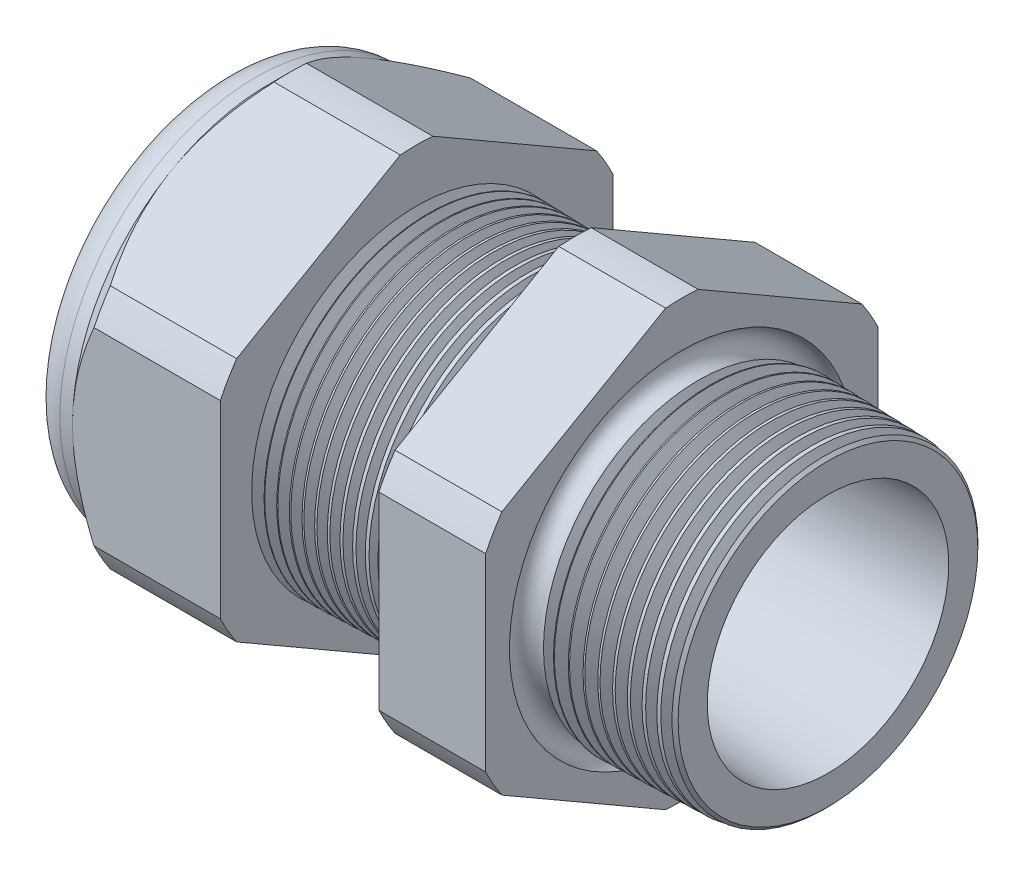
SolidWorks part; units mm, degrees
ref_plane "Front Plane" through (0, 0, 0) normal (0, 0, 1) x (1, 0, 0)
ref_plane "Top Plane" through (0, 0, 0) normal (0, 1, 0) x (1, 0, 0)
ref_plane "Right Plane" through (0, 0, 0) normal (1, 0, 0) x (0, 0, -1)
sketch "Sketch10" plane through (0, 0, 0) normal (0, 0, 1) x (1, 0, 0)
  line L0 (0, 0) -> (-115.3565, 0) construction
  line L1 (-35.814, 5.969) -> (-24.014, 5.969)
  line L2 (1.016, 7.3456) -> (1.016, 9.3776)
  line L3 (-7.874, 9.6104) -> (1.016, 9.3776)
  line L4 (-7.874, 23.876) -> (-7.874, 9.6104)
  line L5 (-7.874, 23.876) -> (-14.374, 23.876)
  line L6 (-14.374, 23.876) -> (-14.374, 9.7806)
  line L7 (-24.014, 10.033) -> (-14.374, 9.7806)
  line L8 (-24.014, 10.033) -> (-24.014, 23.876)
  line L9 (-24.014, 23.876) -> (-33.014, 23.876)
  line L10 (-33.014, 23.876) -> (-33.014, 11.938)
  line L11 (-33.014, 11.938) -> (-35.814, 11.938)
  line L12 (-35.814, 11.938) -> (-35.814, 5.969)
  line L13 (-24.014, 5.969) -> (1.016, 7.3456)
  dimension "D1" = 36.83
  dimension "D2" = 11.938
  dimension "D3" = 1.5
  dimension "D4" = 2.032
  dimension "A" = 20.066
  dimension "D6" = 23.876
  dimension "D8" = 47.752
  dimension "D9" = 2.8
  dimension "D10" = 9
  dimension "D11" = 6.5
  dimension "D" = 8.89
revolve "Revolve2" add sketch "Sketch10" angle 360 about L0
sketch "Sketch12" plane through (-33.014, 0, 0) normal (-1, 0, 0) x (0, 0, 1)
  line L1 (-0.9882, 13.2143) -> (-10.9498, 7.4629)
  line L2 (-11.938, 5.7513) -> (-11.938, -5.7513)
  line L3 (-10.9498, -7.4629) -> (-0.9882, -13.2143)
  line L4 (0.9882, -13.2143) -> (10.9498, -7.4629)
  line L5 (11.938, -5.7513) -> (11.938, 5.7513)
  line L6 (10.9498, 7.4629) -> (0.9882, 13.2143)
  circle A0 centre (0, 0) radius 11.938 construction
  arc A1 (0.9882, 13.2143) -> (-0.9882, 13.2143) centre (0, 0) ccw
  arc A2 (-10.9498, 7.4629) -> (-11.938, 5.7513) centre (0, 0) ccw
  arc A3 (-11.938, -5.7513) -> (-10.9498, -7.4629) centre (0, 0) ccw
  arc A4 (-0.9882, -13.2143) -> (0.9882, -13.2143) centre (0, 0) ccw
  arc A5 (10.9498, -7.4629) -> (11.938, -5.7513) centre (0, 0) ccw
  arc A6 (11.938, 5.7513) -> (10.9498, 7.4629) centre (0, 0) ccw
  dimension "D2" = 26.5024
  dimension "D1" = 23.876
extrude "Cut-Extrude2" cut sketch "Sketch12" against normal through all flip side to cut
fillet "Fillet4" radius 2.032 1 edges at (-35.814, 0, -11.938)
sketch "Sketch19" plane through (-33.014, 0, 0) normal (-1, 0, 0) x (0, 0, 1)
  line L0 (11.938, 0) -> (11.938, 5.7513) construction
  circle A0 centre (0, 0) radius 11.938
extrude "Cut-Extrude3" cut sketch "Sketch19" against normal blind 2 draft 45 flip side to cut
chamfer "Chamfer1" distance 0.254 angle 45 1 edges at (1.016, 0, -9.3776)
sketch "Sketch21" plane through (-35.814, 0, 0) normal (-1, 0, 0) x (0, 0, 1)
  circle A0 centre (0, 0) radius 5.969
  circle A2 centre (0, 0) radius 5.969 construction
extrude "plug" add sketch "Sketch21" against normal blind 6.35 separate body
sketch "Sketch22" plane through (-35.814, 0, 0) normal (-1, 0, 0) x (0, 0, 1)
  circle A0 centre (0, 0) radius 5.715
  circle A1 centre (0, 0) radius 5.969 construction
  dimension "D1" = 0.254
extrude "Cut-Extrude4" cut sketch "Sketch22" against normal blind 0.508
sketch "Sketch27" plane through (-35.306, 0, 0) normal (-1, 0, 0) x (0, 0, 1)
  line L0 (-4.3624, 0) -> (4.3624, 0) construction
  circle A0 centre (-3.6749, 0) radius 2.032
  circle A1 centre (0, 0) radius 5.715 construction
  dimension "D1" = 0.0081
  dimension "holedia" = 4.064
extrude "plugholes" cut sketch "Sketch27" against normal through all
pattern_circular "CirPattern1" count 3 over 360 about axis through (0, 0, 0) along (1, 0, 0) of "plugholes"
sketch "Sketch28" [suppressed] plane through (-29.464, 0, 0) normal (-1, 0, 0) x (0, 0, 1)
  circle A0 centre (0, 0) radius 0.762
  dimension "midholedia" = 4.064
extrude "midhole" [suppressed] cut sketch "Sketch28" against normal through all
sketch "Sketch29" plane through (0, 0, 0) normal (0, 0, 1) x (1, 0, 0)
  line L0 (-24.014, 10.033) -> (-23.281, 10.0138)
  line L1 (-14.374, 9.7806) -> (-24.014, 10.033) construction
  line L2 (-23.281, 10.0138) -> (-23.6641, 9.3886)
  line L3 (-23.6641, 9.3886) -> (-24.014, 10.033)
  dimension "D1" = 60
  dimension "D2" = 60
  dimension "D3" = 0.635
revolve "Cut-Revolve1" cut sketch "Sketch29" angle 360 about axis through (0, 0, 0) along (-1, 0, 0)
pattern_linear "LPattern1" count 13 spacing 0.762 along (1, 0, 0) of "Cut-Revolve1"
sketch "Sketch30" plane through (0, 0, 0) normal (0, 0, 1) x (1, 0, 0)
  line L0 (-7.874, 9.6104) -> (-6.9944, 9.5873)
  line L1 (-7.874, 13.2143) -> (-7.874, 7.4629) construction
  line L2 (0.7621, 9.3842) -> (-7.874, 9.6104) construction
  line L3 (-6.9944, 9.5873) -> (-7.4542, 8.8371)
  line L4 (-7.4542, 8.8371) -> (-7.874, 9.6104)
  dimension "D1" = 60
  dimension "D2" = 60
  dimension "D3" = 0.762
revolve "Cut-Revolve2" cut sketch "Sketch30" angle 360 about axis through (0, 0, 0) along (-1, 0, 0)
pattern_linear "LPattern2" count 10 spacing 0.889 along (1, 0, 0) of "Cut-Revolve2"
sketch "Sketch31" [suppressed] plane through (-38.354, 0, 0) normal (-1, 0, 0) x (0, 0, 1)
  line L0 (-1.905, 1.905) -> (1.905, 1.905)
  line L1 (-1.905, -1.905) -> (1.905, -1.905)
  circle A0 centre (0, 0) radius 1.905 construction
  arc A1 (-1.905, 1.905) -> (-1.905, -1.905) centre (-1.905, 0) ccw
  arc A2 (1.905, 1.905) -> (1.905, -1.905) centre (1.905, 0) cw
extrude "Cut-Extrude5" [suppressed] cut sketch "Sketch31" against normal through all
sketch "Sketch32" plane through (0, 0, 0) normal (0, 0, 1) x (1, 0, 0)
  line L0 (-7.874, 13.2143) -> (-7.874, 7.4629) construction
  circle A0 centre (-7.747, 9.6104) radius 0.889
  dimension "D2" = 1.778
  dimension "D1" = 0.127
revolve "Cut-Revolve3" cut sketch "Sketch32" angle 360 about axis through (0, 0, 0) along (-1, 0, 0)
